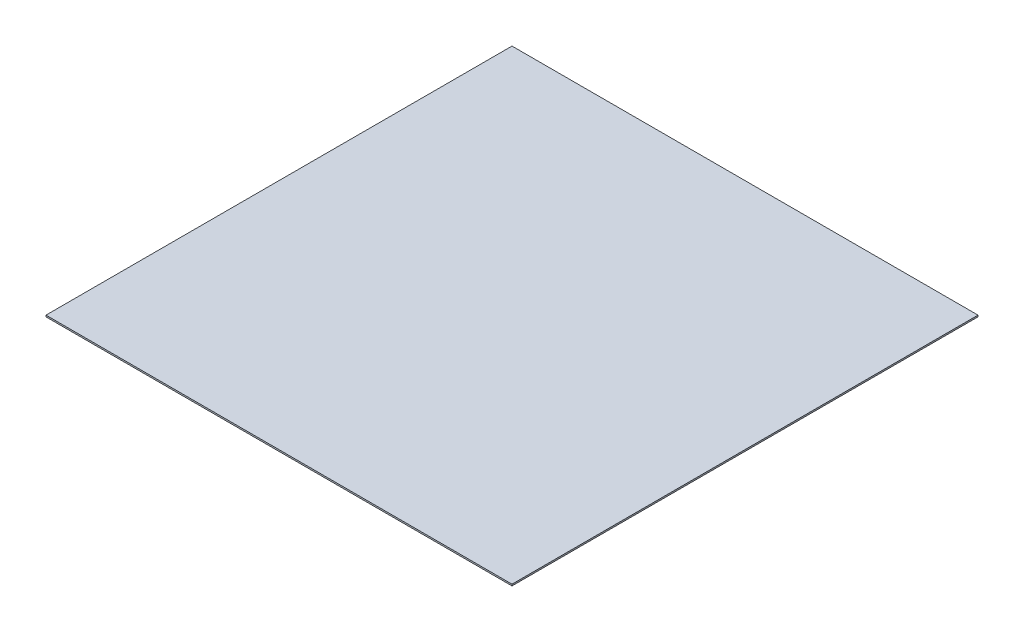
SolidWorks part; units mm, degrees
ref_plane "前视基准面" through (0, 0, 0) normal (0, 0, 1) x (1, 0, 0)
ref_plane "上视基准面" through (0, 0, 0) normal (0, 1, 0) x (1, 0, 0)
ref_plane "右视基准面" through (0, 0, 0) normal (1, 0, 0) x (0, 0, -1)
sketch "草图1" plane through (0, 0, 0) normal (0, 1, 0) x (1, 0, 0)
  line L1 (0, 0) -> (300, 0)
  line L2 (0, 0) -> (0, 300)
  line L3 (0, 300) -> (300, 300)
  line L4 (300, 0) -> (300, 300)
  dimension "D1" = 300
  dimension "D2" = 300
extrude "凸台-拉伸1" add sketch "草图1" along normal blind 1
